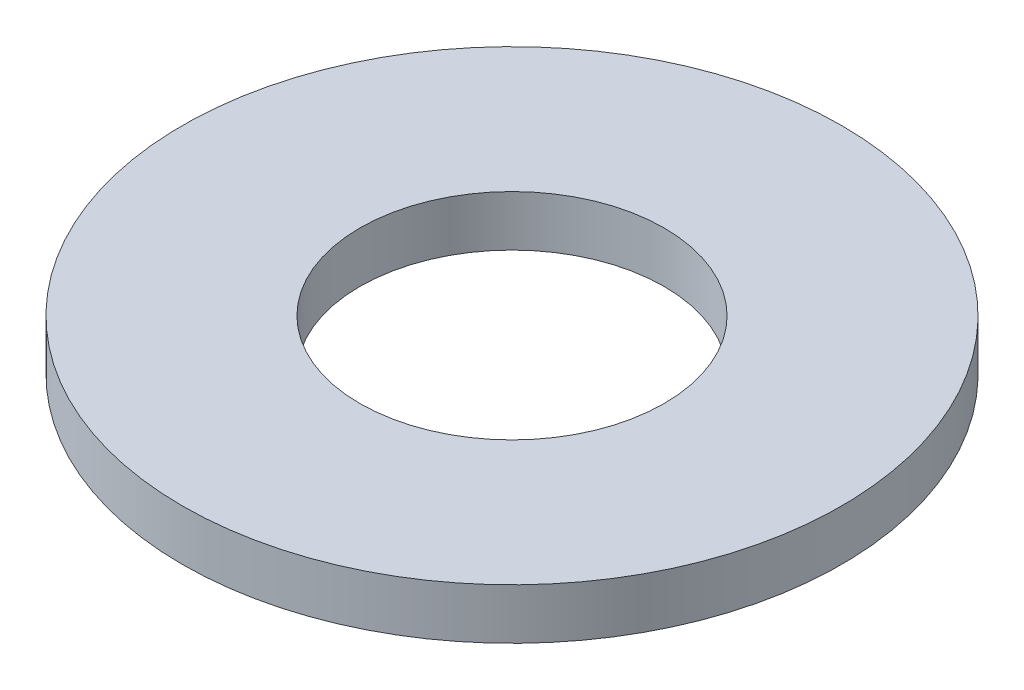
SolidWorks part; units mm, degrees
material "尼龙 101"
ref_plane "前视基准面" through (0, 0, 0) normal (0, 0, 1) x (1, 0, 0)
ref_plane "上视基准面" through (0, 0, 0) normal (0, 1, 0) x (1, 0, 0)
ref_plane "右视基准面" through (0, 0, 0) normal (1, 0, 0) x (0, 0, -1)
sketch "草图1" plane through (0, 0, 0) normal (0, 1, 0) x (1, 0, 0)
  circle A0 centre (0, 0) radius 3
  circle A1 centre (0, 0) radius 6.5
  dimension "D1" = 6
  dimension "D2" = 13
extrude "凸台-拉伸1" add sketch "草图1" along normal blind 1
